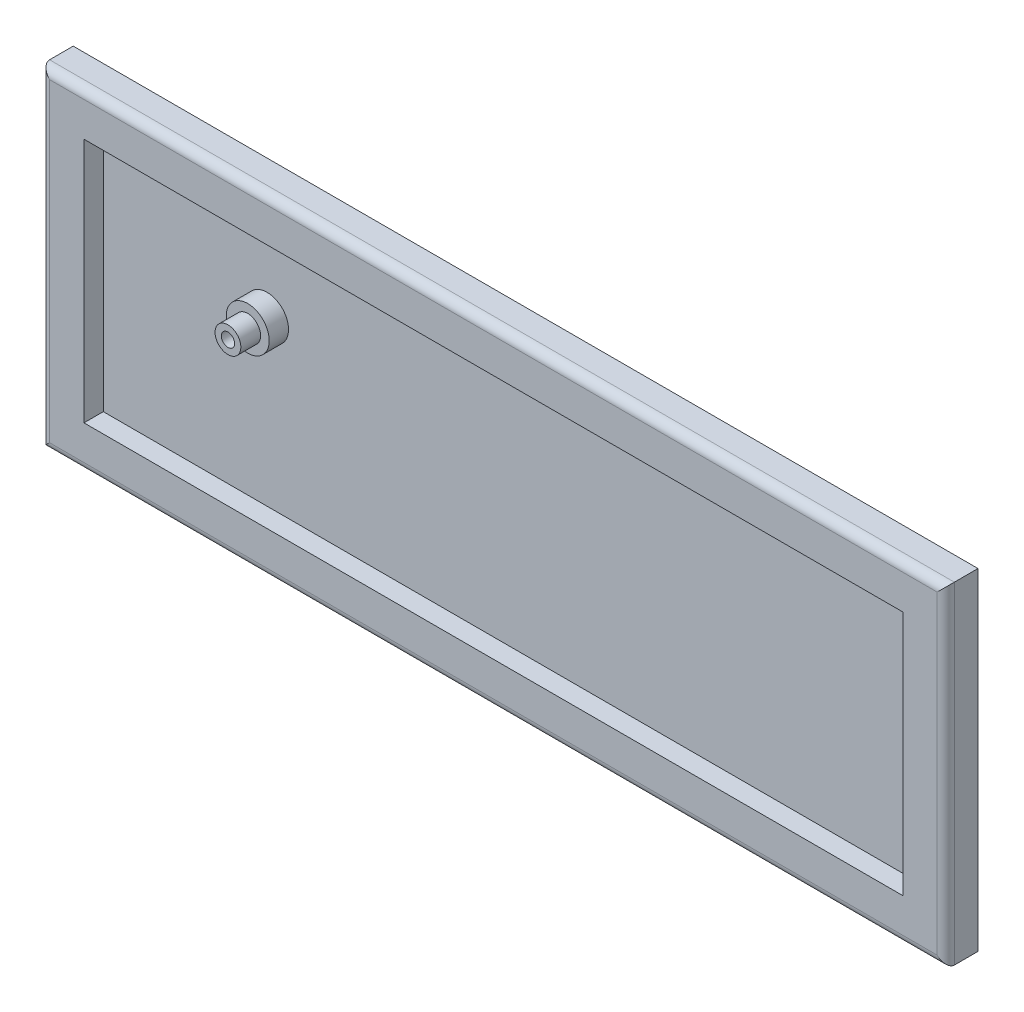
SolidWorks part; units mm, degrees
ref_plane "Front Plane" through (0, 0, 0) normal (0, 0, 1) x (1, 0, 0)
ref_plane "Top Plane" through (0, 0, 0) normal (0, 1, 0) x (1, 0, 0)
ref_plane "Right Plane" through (0, 0, 0) normal (1, 0, 0) x (0, 0, -1)
sketch "Model" plane through (0, 0, 0) normal (0, 0, 1) x (1, 0, 0)
  line L0 (188.597, 57.4075) -> (188.753, 57.4008)
  line L1 (188.753, 57.4008) -> (188.908, 57.3828)
  line L2 (188.908, 57.3828) -> (189.063, 57.3525)
  line L3 (189.063, 57.3525) -> (189.214, 57.3098)
  line L4 (189.214, 57.3098) -> (189.362, 57.2548)
  line L5 (189.362, 57.2548) -> (189.504, 57.1899)
  line L6 (189.504, 57.1899) -> (189.64, 57.113)
  line L7 (189.64, 57.113) -> (189.771, 57.0258)
  line L8 (189.771, 57.0258) -> (189.895, 56.9281)
  line L9 (189.895, 56.9281) -> (190.011, 56.8219)
  line L10 (190.011, 56.8219) -> (190.117, 56.7062)
  line L11 (190.117, 56.7062) -> (190.215, 56.5838)
  line L12 (190.215, 56.5838) -> (190.302, 56.4526)
  line L13 (190.302, 56.4526) -> (190.379, 56.315)
  line L14 (190.379, 56.315) -> (190.444, 56.1728)
  line L15 (190.444, 56.1728) -> (190.499, 56.0268)
  line L16 (190.499, 56.0268) -> (190.54, 55.874)
  line L17 (190.54, 55.874) -> (190.572, 55.7209)
  line L18 (190.572, 55.7209) -> (190.59, 55.5639)
  line L19 (190.59, 55.5639) -> (190.596, 55.4069)
  line L20 (190.596, 55.4069) -> (190.596, 2.2572)
  line L21 (190.596, 2.2572) -> (190.59, 2.1001)
  line L22 (190.59, 2.1001) -> (190.572, 1.9444)
  line L23 (190.572, 1.9444) -> (190.54, 1.7901)
  line L24 (190.54, 1.7901) -> (190.499, 1.6385)
  line L25 (190.499, 1.6385) -> (190.444, 1.491)
  line L26 (190.444, 1.491) -> (190.379, 1.3491)
  line L27 (190.379, 1.3491) -> (190.302, 1.2127)
  line L28 (190.302, 1.2127) -> (190.215, 1.0818)
  line L29 (190.215, 1.0818) -> (190.117, 0.9577)
  line L30 (190.117, 0.9577) -> (190.011, 0.842)
  line L31 (190.011, 0.842) -> (189.895, 0.7359)
  line L32 (189.895, 0.7359) -> (189.771, 0.638)
  line L33 (189.771, 0.638) -> (189.64, 0.5512)
  line L34 (189.64, 0.5512) -> (189.504, 0.474)
  line L35 (189.504, 0.474) -> (189.362, 0.4093)
  line L36 (189.362, 0.4093) -> (189.214, 0.3542)
  line L37 (189.214, 0.3542) -> (189.063, 0.3128)
  line L38 (189.063, 0.3128) -> (188.908, 0.2811)
  line L39 (188.908, 0.2811) -> (188.753, 0.2632)
  line L40 (188.753, 0.2632) -> (188.597, 0.2563)
  line L41 (188.597, 0.2563) -> (2.096, 0.2577)
  line L42 (2.096, 0.2577) -> (1.9389, 0.2632)
  line L43 (1.9389, 0.2632) -> (1.7818, 0.2811)
  line L44 (1.7818, 0.2811) -> (1.6288, 0.3128)
  line L45 (1.6288, 0.3128) -> (1.4759, 0.3542)
  line L46 (1.4759, 0.3542) -> (1.3298, 0.4093)
  line L47 (1.3298, 0.4093) -> (1.1879, 0.474)
  line L48 (1.1879, 0.474) -> (1.0501, 0.5512)
  line L49 (1.0501, 0.5512) -> (0.9192, 0.638)
  line L50 (0.9192, 0.638) -> (0.7965, 0.7359)
  line L51 (0.7965, 0.7359) -> (0.6808, 0.842)
  line L52 (0.6808, 0.842) -> (0.5746, 0.9577)
  line L53 (0.5746, 0.9577) -> (0.4768, 1.0818)
  line L54 (0.4768, 1.0818) -> (0.39, 1.2127)
  line L55 (0.39, 1.2127) -> (0.3128, 1.3491)
  line L56 (0.3128, 1.3491) -> (0.248, 1.491)
  line L57 (0.248, 1.491) -> (0.1929, 1.6385)
  line L58 (0.1929, 1.6385) -> (0.1502, 1.7901)
  line L59 (0.1502, 1.7901) -> (0.1199, 1.9444)
  line L60 (0.1199, 1.9444) -> (0.102, 2.1001)
  line L61 (0.102, 2.1001) -> (0.0951, 2.2572)
  line L62 (0.0951, 2.2572) -> (0.0951, 55.4069)
  line L63 (0.0951, 55.4069) -> (0.102, 55.5639)
  line L64 (0.102, 55.5639) -> (0.1199, 55.7209)
  line L65 (0.1199, 55.7209) -> (0.1502, 55.874)
  line L66 (0.1502, 55.874) -> (0.1929, 56.0268)
  line L67 (0.1929, 56.0268) -> (0.248, 56.1728)
  line L68 (0.248, 56.1728) -> (0.3128, 56.315)
  line L69 (0.3128, 56.315) -> (0.39, 56.4526)
  line L70 (0.39, 56.4526) -> (0.4768, 56.5838)
  line L71 (0.4768, 56.5838) -> (0.5746, 56.7062)
  line L72 (0.5746, 56.7062) -> (0.6808, 56.8219)
  line L73 (0.6808, 56.8219) -> (0.7965, 56.9281)
  line L74 (0.7965, 56.9281) -> (0.9192, 57.0258)
  line L75 (0.9192, 57.0258) -> (1.0501, 57.113)
  line L76 (1.0501, 57.113) -> (1.1879, 57.1899)
  line L77 (1.1879, 57.1899) -> (1.3298, 57.2548)
  line L78 (1.3298, 57.2548) -> (1.4759, 57.3098)
  line L79 (1.4759, 57.3098) -> (1.6288, 57.3525)
  line L80 (1.6288, 57.3525) -> (1.7818, 57.3828)
  line L81 (1.7818, 57.3828) -> (1.9389, 57.4008)
  line L82 (1.9389, 57.4008) -> (2.096, 57.4075)
  line L83 (2.096, 57.4075) -> (188.597, 57.4075)
  line L84 (174.071, 16.7817) -> (188.07, 16.7817)
  line L85 (188.07, 16.7817) -> (188.07, 2.7823)
  line L86 (188.07, 2.7823) -> (174.071, 2.7823)
  line L87 (174.071, 2.7823) -> (174.071, 16.7817)
  line L88 (155.021, 16.7817) -> (169.02, 16.7817)
  line L89 (169.02, 16.7817) -> (169.02, 2.7823)
  line L90 (169.02, 2.7823) -> (155.021, 2.7823)
  line L91 (155.021, 2.7823) -> (155.021, 16.7817)
  line L92 (135.971, 16.7817) -> (149.97, 16.7817)
  line L93 (149.97, 16.7817) -> (149.97, 2.7823)
  line L94 (149.97, 2.7823) -> (135.971, 2.7823)
  line L95 (135.971, 2.7823) -> (135.971, 16.7817)
  line L96 (116.92, 16.7817) -> (130.92, 16.7817)
  line L97 (130.92, 16.7817) -> (130.92, 2.7823)
  line L98 (130.92, 2.7823) -> (116.92, 2.7823)
  line L99 (116.92, 2.7823) -> (116.92, 16.7817)
  line L100 (97.8697, 16.7817) -> (111.869, 16.7817)
  line L101 (111.869, 16.7817) -> (111.869, 2.7823)
  line L102 (111.869, 2.7823) -> (97.8697, 2.7823)
  line L103 (97.8697, 2.7823) -> (97.8697, 16.7817)
  line L104 (78.8211, 16.7817) -> (92.8204, 16.7817)
  line L105 (92.8204, 16.7817) -> (92.8204, 2.7823)
  line L106 (92.8204, 2.7823) -> (78.8211, 2.7823)
  line L107 (78.8211, 2.7823) -> (78.8211, 16.7817)
  line L108 (59.7711, 16.7817) -> (73.7704, 16.7817)
  line L109 (73.7704, 16.7817) -> (73.7704, 2.7823)
  line L110 (73.7704, 2.7823) -> (59.7711, 2.7823)
  line L111 (59.7711, 2.7823) -> (59.7711, 16.7817)
  line L112 (40.7211, 16.7817) -> (54.7204, 16.7817)
  line L113 (54.7204, 16.7817) -> (54.7204, 2.7823)
  line L114 (54.7204, 2.7823) -> (40.7211, 2.7823)
  line L115 (40.7211, 2.7823) -> (40.7211, 16.7817)
  line L116 (21.671, 16.7817) -> (35.6704, 16.7817)
  line L117 (35.6704, 16.7817) -> (35.6704, 2.7823)
  line L118 (35.6704, 2.7823) -> (21.671, 2.7823)
  line L119 (21.671, 2.7823) -> (21.671, 16.7817)
  line L120 (2.621, 16.7817) -> (16.6205, 16.7817)
  line L121 (16.6205, 16.7817) -> (16.6205, 2.7823)
  line L122 (16.6205, 2.7823) -> (2.621, 2.7823)
  line L123 (2.621, 2.7823) -> (2.621, 16.7817)
  line L124 (174.071, 35.8316) -> (188.07, 35.8316)
  line L125 (188.07, 35.8316) -> (188.07, 21.8323)
  line L126 (188.07, 21.8323) -> (174.071, 21.8323)
  line L127 (174.071, 21.8323) -> (174.071, 35.8316)
  line L128 (155.021, 35.8316) -> (169.02, 35.8316)
  line L129 (169.02, 35.8316) -> (169.02, 21.8323)
  line L130 (169.02, 21.8323) -> (155.021, 21.8323)
  line L131 (155.021, 21.8323) -> (155.021, 35.8316)
  line L132 (135.971, 35.8316) -> (149.97, 35.8316)
  line L133 (149.97, 35.8316) -> (149.97, 21.8323)
  line L134 (149.97, 21.8323) -> (135.971, 21.8323)
  line L135 (135.971, 21.8323) -> (135.971, 35.8316)
  line L136 (116.92, 35.8316) -> (130.92, 35.8316)
  line L137 (130.92, 35.8316) -> (130.92, 21.8323)
  line L138 (130.92, 21.8323) -> (116.92, 21.8323)
  line L139 (116.92, 21.8323) -> (116.92, 35.8316)
  line L140 (97.8697, 35.8316) -> (111.869, 35.8316)
  line L141 (111.869, 35.8316) -> (111.869, 21.8323)
  line L142 (111.869, 21.8323) -> (97.8697, 21.8323)
  line L143 (97.8697, 21.8323) -> (97.8697, 35.8316)
  line L144 (78.8211, 35.8316) -> (92.8204, 35.8316)
  line L145 (92.8204, 35.8316) -> (92.8204, 21.8323)
  line L146 (92.8204, 21.8323) -> (78.8211, 21.8323)
  line L147 (78.8211, 21.8323) -> (78.8211, 35.8316)
  line L148 (59.7711, 35.8316) -> (73.7704, 35.8316)
  line L149 (73.7704, 35.8316) -> (73.7704, 21.8323)
  line L150 (73.7704, 21.8323) -> (59.7711, 21.8323)
  line L151 (59.7711, 21.8323) -> (59.7711, 35.8316)
  line L152 (40.7211, 35.8316) -> (54.7204, 35.8316)
  line L153 (54.7204, 35.8316) -> (54.7204, 21.8323)
  line L154 (54.7204, 21.8323) -> (40.7211, 21.8323)
  line L155 (40.7211, 21.8323) -> (40.7211, 35.8316)
  line L156 (21.671, 35.8316) -> (35.6704, 35.8316)
  line L157 (35.6704, 35.8316) -> (35.6704, 21.8323)
  line L158 (35.6704, 21.8323) -> (21.671, 21.8323)
  line L159 (21.671, 21.8323) -> (21.671, 35.8316)
  line L160 (2.621, 35.8316) -> (16.6205, 35.8316)
  line L161 (16.6205, 35.8316) -> (16.6205, 21.8323)
  line L162 (16.6205, 21.8323) -> (2.621, 21.8323)
  line L163 (2.621, 21.8323) -> (2.621, 35.8316)
  line L164 (174.071, 54.8816) -> (188.07, 54.8816)
  line L165 (188.07, 54.8816) -> (188.07, 40.8824)
  line L166 (188.07, 40.8824) -> (174.071, 40.8824)
  line L167 (174.071, 40.8824) -> (174.071, 54.8816)
  line L168 (155.021, 54.8816) -> (169.02, 54.8816)
  line L169 (169.02, 54.8816) -> (169.02, 40.8824)
  line L170 (169.02, 40.8824) -> (155.021, 40.8824)
  line L171 (155.021, 40.8824) -> (155.021, 54.8816)
  line L172 (135.971, 54.8816) -> (149.97, 54.8816)
  line L173 (149.97, 54.8816) -> (149.97, 40.8824)
  line L174 (149.97, 40.8824) -> (135.971, 40.8824)
  line L175 (135.971, 40.8824) -> (135.971, 54.8816)
  line L176 (116.92, 54.8816) -> (130.92, 54.8816)
  line L177 (130.92, 54.8816) -> (130.92, 40.8824)
  line L178 (130.92, 40.8824) -> (116.92, 40.8824)
  line L179 (116.92, 40.8824) -> (116.92, 54.8816)
  line L180 (97.8697, 54.8816) -> (111.869, 54.8816)
  line L181 (111.869, 54.8816) -> (111.869, 40.8824)
  line L182 (111.869, 40.8824) -> (97.8697, 40.8824)
  line L183 (97.8697, 40.8824) -> (97.8697, 54.8816)
  line L184 (78.8211, 54.8816) -> (92.8204, 54.8816)
  line L185 (92.8204, 54.8816) -> (92.8204, 40.8824)
  line L186 (92.8204, 40.8824) -> (78.8211, 40.8824)
  line L187 (78.8211, 40.8824) -> (78.8211, 54.8816)
  line L188 (59.7711, 54.8816) -> (73.7704, 54.8816)
  line L189 (73.7704, 54.8816) -> (73.7704, 40.8824)
  line L190 (73.7704, 40.8824) -> (59.7711, 40.8824)
  line L191 (59.7711, 40.8824) -> (59.7711, 54.8816)
  line L192 (40.7211, 54.8816) -> (54.7204, 54.8816)
  line L193 (54.7204, 54.8816) -> (54.7204, 40.8824)
  line L194 (54.7204, 40.8824) -> (40.7211, 40.8824)
  line L195 (40.7211, 40.8824) -> (40.7211, 54.8816)
  line L196 (21.671, 54.8816) -> (35.6704, 54.8816)
  line L197 (35.6704, 54.8816) -> (35.6704, 40.8824)
  line L198 (35.6704, 40.8824) -> (21.671, 40.8824)
  line L199 (21.671, 40.8824) -> (21.671, 54.8816)
  line L200 (2.621, 54.8816) -> (16.6205, 54.8816)
  line L201 (16.6205, 54.8816) -> (16.6205, 40.8824)
  line L202 (16.6205, 40.8824) -> (2.621, 40.8824)
  line L203 (2.621, 40.8824) -> (2.621, 54.8816)
sketch "草图2" plane through (0, 0, 0) normal (0, 0, 1) x (1, 0, 0)
  line L0 (0.0951, 28.8321) -> (190.596, 28.8321) construction
  line L1 (0.0951, 2.2572) -> (0.0951, 55.4069) construction
  line L2 (190.596, 55.4069) -> (190.596, 2.2572) construction
  line L3 (95.3465, 57.4075) -> (95.3465, 0.257) construction
  line L4 (2.096, 57.4075) -> (188.597, 57.4075) construction
  line L5 (188.597, 0.2563) -> (2.096, 0.2577) construction
  line L7 (200.596, -9.7432) -> (-9.9049, -9.7432)
  line L8 (200.596, -9.7432) -> (200.596, 67.4073)
  line L9 (200.596, 67.4073) -> (-9.9049, 67.4073)
  line L10 (-9.9049, -9.7432) -> (-9.9049, 67.4073)
  line L11 (200.596, -9.7432) -> (-9.9049, 67.4073) construction
  line L12 (200.596, 67.4073) -> (-9.9049, -9.7432) construction
  point P12 (95.3455, 28.8321)
  dimension "D1" = 190.5009
  dimension "D2" = 57.1505
  dimension "D3" = 77.1505
  dimension "D4" = 210.5009
extrude "凸台-拉伸1" add sketch "草图2" along normal blind 34.5
shell "抽壳1" thickness 10
sketch "草图3" plane through (0, 0, 0) normal (0, 0, 1) x (1, 0, 0)
  line L3 (35.6704, 21.8323) -> (40.7211, 16.7817) construction
  line L4 (40.7211, 16.7817) -> (40.7211, 21.8323) construction
  line L5 (40.7211, 21.8323) -> (35.6704, 16.7817) construction
  line L6 (149.97, 35.8316) -> (155.021, 40.8824) construction
  line L8 (149.97, 16.7817) -> (155.021, 21.8323) construction
  circle A0 centre (152.4955, 38.357) radius 2.7421
  circle A1 centre (152.4955, 19.1108) radius 3.3242
  circle A2 centre (38.1958, 38.357) radius 2.1
  circle A3 centre (38.1958, 19.307) radius 2.8734
  dimension "D1" = 4.2
extrude "切除-拉伸8" cut sketch "草图3" along normal blind 7.6 contours A2
sketch "草图4" plane through (0, 0, 3) normal (0, 0, 1) x (1, 0, 0)
  circle A0 centre (38.1958, 38.357) radius 5
  dimension "D1" = 10
extrude "凸台-拉伸2" add sketch "草图4" along normal blind 9.1 contours A0
sketch "草图6" plane through (0, 0, 12.1) normal (0, 0, 1) x (1, 0, 0)
  circle A0 centre (38.1958, 38.357) radius 1.55
  dimension "D1" = 3.1
extrude "切除-拉伸9" cut sketch "草图6" against normal blind 9.1 contours A0
sketch "草图10" plane through (0, 0, 0) normal (0, 0, 1) x (1, 0, 0)
  circle A0 centre (38.1958, 38.357) radius 3
  dimension "D1" = 6
extrude "切除-拉伸16" cut sketch "草图10" against normal blind 4.6 from surface at 12.1 flip side to cut contours A0 starting at face at (39.7458, 38.357, 12.1)
fillet "圆角1" radius 2 4 edges at (95.3455, 67.4073, 7.5) (200.596, 28.8321, 7.5) (95.3455, -9.7432, 7.5) (-9.9049, 28.8321, 7.5)
